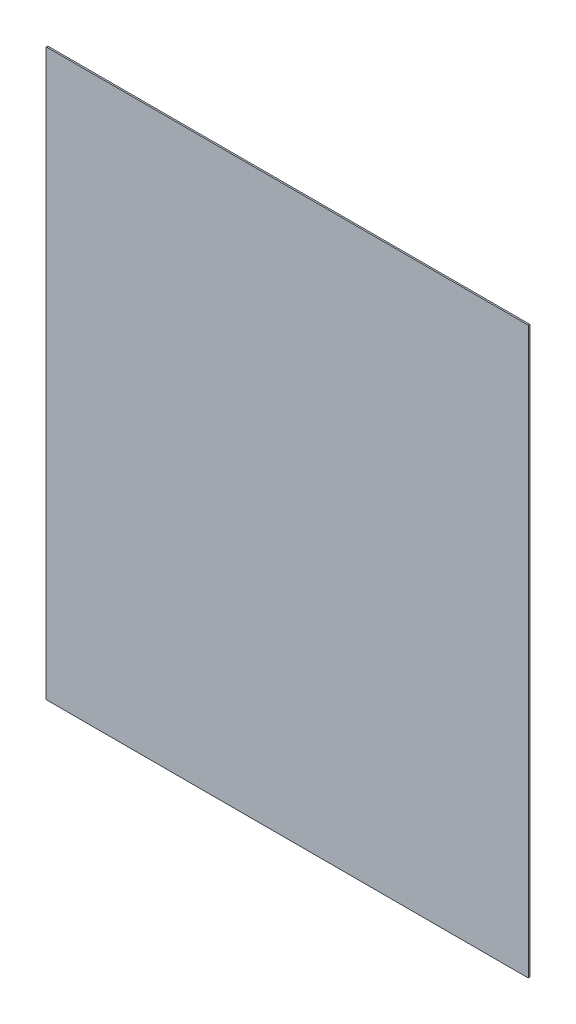
SolidWorks part; units mm, degrees
ref_plane "Plan de face" through (0, 0, 0) normal (0, 0, 1) x (1, 0, 0)
ref_plane "Plan de dessus" through (0, 0, 0) normal (0, 1, 0) x (1, 0, 0)
ref_plane "Plan de droite" through (0, 0, 0) normal (1, 0, 0) x (0, 0, -1)
sketch "Sketch1" plane through (0, 0, 0) normal (0, 0, 1) x (1, 0, 0)
  line L1 (0, 0) -> (324, 0)
  line L2 (0, 0) -> (0, 380)
  line L3 (0, 380) -> (324, 380)
  line L4 (324, 0) -> (324, 380)
  dimension "D1" = 324
  dimension "D2" = 380
extrude "Boss-Extrude1" add sketch "Sketch1" along normal blind 1
